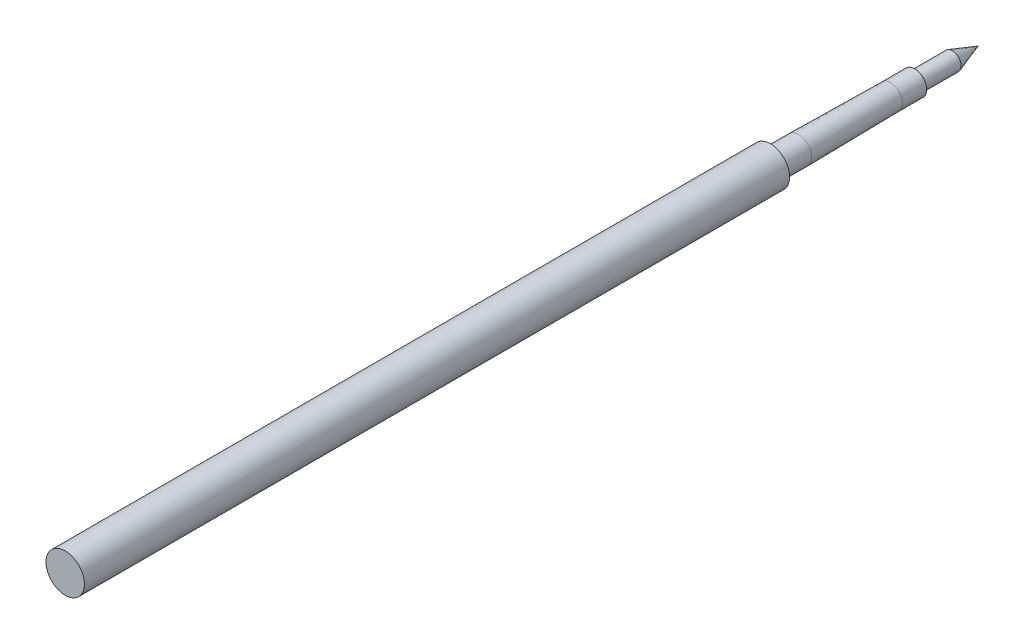
SolidWorks part; units mm, degrees
ref_plane "前视基准面" through (0, 0, 0) normal (0, 0, 1) x (1, 0, 0)
ref_plane "上视基准面" through (0, 0, 0) normal (0, 1, 0) x (1, 0, 0)
ref_plane "右视基准面" through (0, 0, 0) normal (1, 0, 0) x (0, 0, -1)
sketch "草图1" plane through (0, 0, 0) normal (0, 1, 0) x (1, 0, 0)
  line L0 (0, 0) -> (0, 129.006) construction
  line L1 (0, 0) -> (-2.4, 0)
  line L2 (-2.4, 0) -> (-2.4, 88)
  line L3 (-2.4, 88) -> (-1.65, 88)
  line L4 (-1.65, 88) -> (-1.65, 91.5)
  line L5 (-1.65, 91.5) -> (-1.5, 103)
  line L6 (-1.5, 103) -> (-1.5, 106)
  line L7 (-1.5, 106) -> (-1.1, 106)
  line L8 (-1.1, 106) -> (-1.1, 110.7)
  line L9 (-1.1, 110.7) -> (0, 113.9)
  line L10 (0, 0) -> (0, 113.9)
  dimension "D1" = 88
  dimension "D2" = 4.8
  dimension "D3" = 3.3
  dimension "D4" = 3
  dimension "D5" = 3
  dimension "D6" = 3.5
  dimension "D7" = 18
  dimension "D8" = 4.7
  dimension "D9" = 7.9
  dimension "D10" = 2.2
revolve "旋转1" add sketch "草图1" angle 360 about L0
